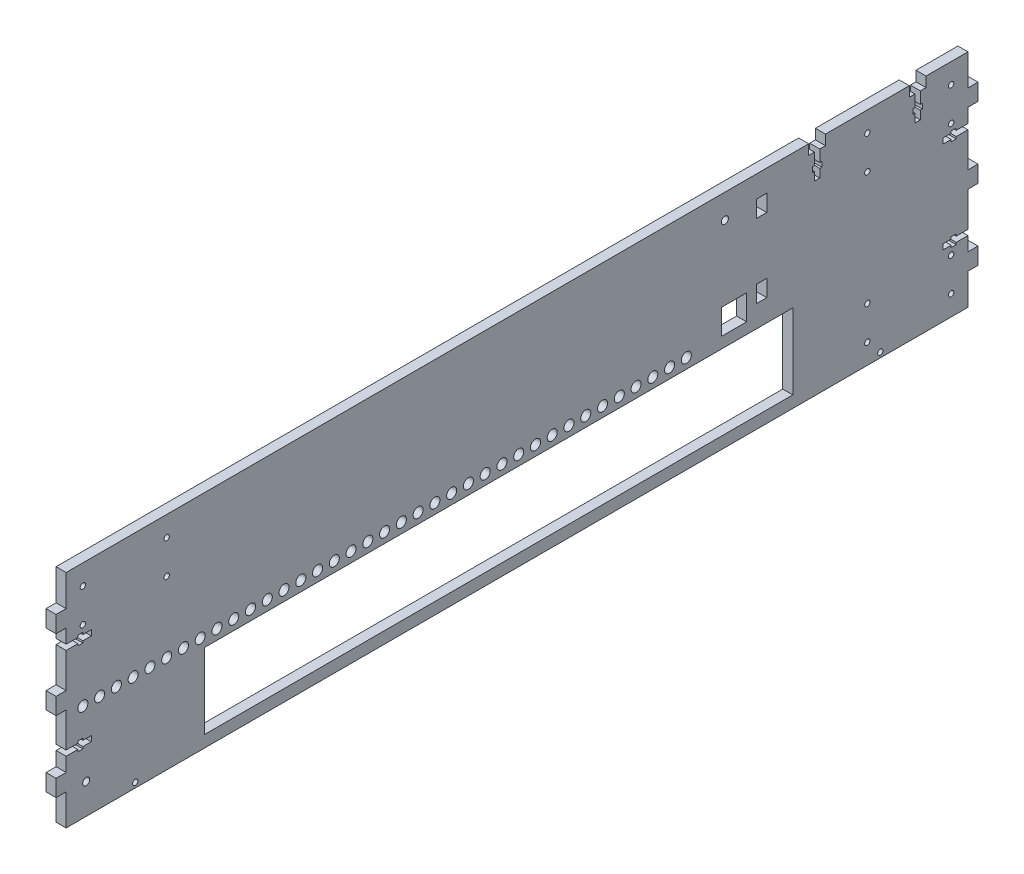
SolidWorks part; units mm, degrees
ref_plane "Front Plane" through (0, 0, 0) normal (0, 0, 1) x (1, 0, 0)
ref_plane "Top Plane" through (0, 0, 0) normal (0, 1, 0) x (1, 0, 0)
ref_plane "Right Plane" through (0, 0, 0) normal (1, 0, 0) x (0, 0, -1)
sketch "Sketch1" plane through (0, 0, 0) normal (1, 0, 0) x (0, 0, -1)
  line L1 (-269, -66) -> (269, -66)
  line L2 (-269, -66) -> (-269, 66)
  line L3 (-269, 66) -> (269, 66)
  line L4 (269, -66) -> (269, 66)
  line L5 (-269, -66) -> (269, 66) construction
  line L6 (-269, 66) -> (269, -66) construction
  point P0 (0, 0)
  dimension "D1" = 132
  dimension "D2" = 538
extrude "Boss-Extrude1" add sketch "Sketch1" along normal blind 6
sketch "Sketch4" plane through (0, 0, 269) normal (0, 0, 1) x (1, 0, 0)
  line L0 (0, 66) -> (0, -66) construction
  line L1 (0, 47.3321) -> (6, 47.3321)
  line L2 (0, 47.3321) -> (0, 37.3321)
  line L3 (0, 37.3321) -> (6, 37.3321)
  line L4 (6, 47.3321) -> (6, 37.3321)
  line L5 (6, 66) -> (6, -66) construction
  line L6 (0, 37.3321) -> (6, 37.3321) construction
  line L7 (0, -66) -> (0, 66) construction
  line L8 (6, 47.3321) -> (0, 47.3321) construction
  line L9 (0, -5) -> (6, -5) construction
  line L10 (0, -5) -> (6, -5)
  line L11 (0, -5) -> (0, 5)
  line L12 (0, 5) -> (6, 5)
  line L13 (6, -5) -> (6, 5)
  line L14 (6, -66) -> (6, 66) construction
  line L15 (6, 5) -> (0, 5) construction
  line L16 (6, -37.3321) -> (0, -37.3321) construction
  line L17 (0, -47.3321) -> (6, -47.3321)
  line L18 (0, -47.3321) -> (0, -37.3321)
  line L19 (0, -37.3321) -> (6, -37.3321)
  line L20 (6, -47.3321) -> (6, -37.3321)
  line L21 (0, -47.3321) -> (6, -47.3321) construction
extrude "Boss-Extrude2" add sketch "Sketch4" along normal blind 6 contours L11 L12 L13 L10
sketch "Sketch5" plane through (0, 0, 0) normal (-1, 0, 0) x (0, 0, 1)
  line L1 (269, 28.9321) -> (269, 25.7321) construction
  line L3 (269, 28.9321) -> (269, 25.7321) construction
  line L4 (269, -25.7321) -> (269, -28.9321) construction
  line L5 (269, -25.7321) -> (269, -28.9321) construction
  line L6 (269, 27.3321) -> (254, 27.3321) construction
  line L7 (269, -27.3321) -> (254, -27.3321) construction
  line L8 (269, -25.7321) -> (262, -25.7321)
  line L9 (269, 28.9321) -> (262, 28.9321)
  line L10 (269, -28.9321) -> (262, -28.9321)
  line L11 (269, 25.7321) -> (262, 25.7321)
  line L12 (269, -25.7321) -> (269, -28.9321)
  line L13 (254, -25.7321) -> (254, -28.9321)
  line L14 (269, 28.9321) -> (269, 25.7321)
  line L15 (254, 28.9321) -> (254, 25.7321)
  line L16 (259, 25.7321) -> (254, 25.7321)
  line L17 (262, 24.5321) -> (259, 24.5321)
  line L18 (262, 24.5321) -> (262, 25.7321)
  line L19 (262, 30.1321) -> (259, 30.1321)
  line L20 (259, 24.5321) -> (259, 25.7321)
  line L21 (262, 24.5321) -> (259, 30.1321) construction
  line L22 (262, 30.1321) -> (259, 24.5321) construction
  line L23 (262, -30.1321) -> (259, -30.1321)
  line L24 (262, -30.1321) -> (262, -28.9321)
  line L25 (262, -24.5321) -> (259, -24.5321)
  line L26 (259, -30.1321) -> (259, -28.9321)
  line L27 (262, -30.1321) -> (259, -24.5321) construction
  line L28 (262, -24.5321) -> (259, -30.1321) construction
  line L29 (269, 25.7321) -> (254, 25.7321) construction
  line L30 (262, 28.9321) -> (262, 30.1321)
  line L31 (259, 28.9321) -> (254, 28.9321)
  line L32 (269, 28.9321) -> (254, 28.9321) construction
  line L33 (259, 28.9321) -> (259, 30.1321)
  line L34 (259, -25.7321) -> (254, -25.7321)
  line L35 (269, -25.7321) -> (254, -25.7321) construction
  line L36 (259, -25.7321) -> (259, -24.5321)
  line L37 (259, -28.9321) -> (254, -28.9321)
  line L38 (269, -28.9321) -> (254, -28.9321) construction
  line L39 (262, -25.7321) -> (262, -24.5321)
  point P20 (260.5, 27.3321)
  point P25 (260.5, -27.3321)
  dimension "D3" = 1.6
  dimension "D4" = 7
  dimension "D5" = 3
  dimension "D6" = 5.6
  dimension "D1" = 15
  dimension "D7" = 7
  dimension "D8" = 3
  dimension "D9" = 5.6
  dimension "D2" = 1.6
extrude "Cut-Extrude3" cut sketch "Sketch5" against normal up to next
sketch "Sketch6" plane through (0, 0, -269) normal (0, 0, -1) x (-1, 0, 0)
  line L0 (0, 47.3321) -> (0, 37.3321) construction
  line L1 (0, 37.3321) -> (-6, 37.3321) construction
  line L2 (-6, 37.3321) -> (-6, 47.3321) construction
  line L3 (-6, 47.3321) -> (0, 47.3321) construction
  line L4 (0, 5) -> (0, -5) construction
  line L5 (0, -5) -> (-6, -5) construction
  line L6 (-6, -5) -> (-6, 5) construction
  line L7 (-6, 5) -> (0, 5) construction
  line L8 (0, -37.3321) -> (0, -47.3321) construction
  line L9 (0, -47.3321) -> (-6, -47.3321) construction
  line L10 (-6, -47.3321) -> (-6, -37.3321) construction
  line L11 (-6, -37.3321) -> (0, -37.3321) construction
  line L12 (0, 47.3321) -> (0, 37.3321)
  line L13 (0, 37.3321) -> (-6, 37.3321)
  line L14 (-6, 37.3321) -> (-6, 47.3321)
  line L15 (-6, 47.3321) -> (0, 47.3321)
  line L16 (0, 5) -> (0, -5)
  line L17 (0, -5) -> (-6, -5)
  line L18 (-6, -5) -> (-6, 5)
  line L19 (-6, 5) -> (0, 5)
  line L20 (0, -37.3321) -> (0, -47.3321)
  line L21 (0, -47.3321) -> (-6, -47.3321)
  line L22 (-6, -47.3321) -> (-6, -37.3321)
  line L23 (-6, -37.3321) -> (0, -37.3321)
extrude "Boss-Extrude3" add sketch "Sketch6" along normal blind 6
sketch "Sketch7" plane through (0, 0, 0) normal (-1, 0, 0) x (0, 0, 1)
  line L0 (262, 25.7321) -> (269, 25.7321) construction
  line L2 (262, 25.7321) -> (262, 24.5321) construction
  line L3 (259, 24.5321) -> (262, 24.5321) construction
  line L4 (259, 25.7321) -> (259, 24.5321) construction
  line L5 (254, 25.7321) -> (259, 25.7321) construction
  line L6 (254, 25.7321) -> (254, 28.9321) construction
  line L7 (254, 28.9321) -> (259, 28.9321) construction
  line L8 (259, 30.1321) -> (259, 28.9321) construction
  line L9 (259, 30.1321) -> (262, 30.1321) construction
  line L10 (262, 30.1321) -> (262, 28.9321) construction
  line L11 (262, 28.9321) -> (269, 28.9321) construction
  line L12 (262, 25.7321) -> (269, 25.7321) construction
  line L13 (262, 25.7321) -> (262, 24.5321) construction
  line L14 (259, 24.5321) -> (262, 24.5321) construction
  line L15 (259, 25.7321) -> (259, 24.5321) construction
  line L16 (254, 25.7321) -> (259, 25.7321) construction
  line L17 (254, 25.7321) -> (254, 28.9321) construction
  line L18 (254, 28.9321) -> (259, 28.9321) construction
  line L19 (259, 30.1321) -> (259, 28.9321) construction
  line L20 (259, 30.1321) -> (262, 30.1321) construction
  line L21 (262, 30.1321) -> (262, 28.9321) construction
  line L22 (262, 28.9321) -> (269, 28.9321) construction
  line L23 (254, -28.9321) -> (259, -28.9321) construction
  line L24 (259, -28.9321) -> (259, -30.1321) construction
  line L25 (259, -30.1321) -> (262, -30.1321) construction
  line L26 (262, -28.9321) -> (262, -30.1321) construction
  line L27 (262, -28.9321) -> (269, -28.9321) construction
  line L28 (262, -25.7321) -> (269, -25.7321) construction
  line L29 (262, -24.5321) -> (262, -25.7321) construction
  line L30 (259, -24.5321) -> (262, -24.5321) construction
  line L31 (259, -24.5321) -> (259, -25.7321) construction
  line L32 (254, -25.7321) -> (259, -25.7321) construction
  line L33 (254, -28.9321) -> (254, -25.7321) construction
  line L34 (254, -28.9321) -> (259, -28.9321) construction
  line L35 (259, -28.9321) -> (259, -30.1321) construction
  line L36 (259, -30.1321) -> (262, -30.1321) construction
  line L37 (262, -28.9321) -> (262, -30.1321) construction
  line L38 (262, -28.9321) -> (269, -28.9321) construction
  line L39 (262, -25.7321) -> (269, -25.7321) construction
  line L40 (262, -24.5321) -> (262, -25.7321) construction
  line L41 (259, -24.5321) -> (262, -24.5321) construction
  line L42 (259, -24.5321) -> (259, -25.7321) construction
  line L43 (254, -25.7321) -> (259, -25.7321) construction
  line L44 (254, -28.9321) -> (254, -25.7321) construction
  line L45 (0, 0) -> (0, 57.5645) construction
  line L46 (-254, -28.9321) -> (-254, -25.7321)
  line L47 (-254, -25.7321) -> (-259, -25.7321)
  line L48 (-259, -24.5321) -> (-259, -25.7321)
  line L49 (-259, -24.5321) -> (-262, -24.5321)
  line L50 (-262, -24.5321) -> (-262, -25.7321)
  line L51 (-262, -25.7321) -> (-269, -25.7321)
  line L52 (-262, -28.9321) -> (-269, -28.9321)
  line L53 (-262, -28.9321) -> (-262, -30.1321)
  line L54 (-259, -30.1321) -> (-262, -30.1321)
  line L55 (-259, -28.9321) -> (-259, -30.1321)
  line L56 (-254, -28.9321) -> (-259, -28.9321)
  line L57 (-262, 28.9321) -> (-269, 28.9321)
  line L58 (-262, 30.1321) -> (-262, 28.9321)
  line L59 (-259, 30.1321) -> (-262, 30.1321)
  line L60 (-259, 30.1321) -> (-259, 28.9321)
  line L61 (-254, 28.9321) -> (-259, 28.9321)
  line L62 (-254, 25.7321) -> (-254, 28.9321)
  line L63 (-254, 25.7321) -> (-259, 25.7321)
  line L64 (-259, 25.7321) -> (-259, 24.5321)
  line L65 (-259, 24.5321) -> (-262, 24.5321)
  line L66 (-262, 25.7321) -> (-262, 24.5321)
  line L67 (-262, 25.7321) -> (-269, 25.7321)
  line L68 (-269, 28.9321) -> (-269, 25.7321)
  line L69 (-269, -25.7321) -> (-269, -28.9321)
extrude "Cut-Extrude4" cut sketch "Sketch7" against normal up to next
sketch "Sketch8" plane through (0, 0, 0) normal (-1, 0, 0) x (0, 0, 1)
  line L0 (186, -14.55) -> (-164, -14.55) construction
  line L1 (186, -14.55) -> (-164, -14.55) construction
  line L2 (186, -14.55) -> (186, -59) construction
  line L3 (186, -14.55) -> (186, -59) construction
  line L186 (-164, -14.55) -> (-164, -59) construction
  line L187 (-164, -59) -> (186, -59) construction
  line L188 (186.5, -14.05) -> (186.5, -59)
  line L189 (186.5, -14.05) -> (-164.5, -14.05)
  line L190 (-164.5, -14.05) -> (-164.5, -59)
  line L191 (-164.5, -59) -> (186.5, -59)
  dimension "D1" = 0.5
extrude "Cut-Extrude5" cut sketch "Sketch8" against normal up to next
sketch "Sketch11" plane through (6, 0, 0) normal (1, 0, 0) x (0, 0, -1)
  line L0 (149, 43) -> (149, 53) construction
  line L1 (149, 53) -> (143, 53) construction
  line L2 (143, 53) -> (143, 43) construction
  line L3 (143, 43) -> (149, 43) construction
  line L4 (149, -1) -> (149, 9) construction
  line L5 (149, 9) -> (143, 9) construction
  line L6 (143, 9) -> (143, -1) construction
  line L7 (143, -1) -> (149, -1) construction
  line L8 (149, 43) -> (149, 53)
  line L9 (149, 53) -> (143, 53)
  line L10 (143, 53) -> (143, 43)
  line L11 (143, 43) -> (149, 43)
  line L12 (149, -1) -> (149, 9)
  line L13 (149, 9) -> (143, 9)
  line L14 (143, 9) -> (143, -1)
  line L15 (143, -1) -> (149, -1)
extrude "Cut-Extrude8" cut sketch "Sketch11" against normal up to next
sketch "Sketch12" plane through (0, 0, 0) normal (-1, 0, 0) x (0, 0, 1)
  line L0 (-143, 53) -> (-143, 43) construction
  line L1 (-269, 66) -> (269, 66) construction
  circle A0 centre (-124, 51.5) radius 2.1
  dimension "D1" = 19
  dimension "D3" = 4.2
  dimension "D2" = 14.5
extrude "Cut-Extrude9" cut sketch "Sketch12" against normal up to next
sketch "Sketch13" plane through (0, 66, 0) normal (0, 1, 0) x (1, 0, 0)
  line L0 (6, 269) -> (6, -269) construction
  line L1 (0, 234) -> (6, 234)
  line L2 (0, 234) -> (0, 244)
  line L3 (0, 244) -> (6, 244)
  line L4 (6, 234) -> (6, 244)
  line L5 (0, 234) -> (6, 244) construction
  line L6 (0, 244) -> (6, 234) construction
  line L7 (6, 244) -> (0, 244) construction
  line L8 (6, 184) -> (0, 184) construction
  line L9 (0, 174) -> (6, 174)
  line L10 (0, 174) -> (0, 184)
  line L11 (0, 184) -> (6, 184)
  line L12 (6, 174) -> (6, 184)
  line L13 (0, 174) -> (6, 184) construction
  line L14 (0, 184) -> (6, 174) construction
  point P0 (3, 239)
  point P10 (3, 179)
extrude "Cut-Extrude10" cut sketch "Sketch13" against normal blind 6
sketch "Sketch14" plane through (0, 0, 0) normal (-1, 0, 0) x (0, 0, 1)
  circle A0 centre (259, -8) radius 3 construction
  circle A1 centre (259, -8) radius 3
  circle A2 centre (249, -8) radius 3
  circle A3 centre (239, -8) radius 3
  circle A4 centre (229, -8) radius 3
  circle A5 centre (219, -8) radius 3
  circle A6 centre (209, -8) radius 3
  circle A7 centre (199, -8) radius 3
  circle A8 centre (189, -8) radius 3
  circle A9 centre (179, -8) radius 3
  circle A10 centre (169, -8) radius 3
  circle A11 centre (159, -8) radius 3
  circle A12 centre (149, -8) radius 3
  circle A13 centre (139, -8) radius 3
  circle A14 centre (129, -8) radius 3
  circle A15 centre (119, -8) radius 3
  circle A16 centre (109, -8) radius 3
  circle A17 centre (99, -8) radius 3
  circle A18 centre (89, -8) radius 3
  circle A19 centre (79, -8) radius 3
  circle A20 centre (69, -8) radius 3
  circle A21 centre (59, -8) radius 3
  circle A22 centre (49, -8) radius 3
  circle A23 centre (39, -8) radius 3
  circle A24 centre (29, -8) radius 3
  circle A25 centre (19, -8) radius 3
  circle A26 centre (9, -8) radius 3
  circle A27 centre (-1, -8) radius 3
  circle A28 centre (-11, -8) radius 3
  circle A29 centre (-21, -8) radius 3
  circle A30 centre (-31, -8) radius 3
  circle A31 centre (-41, -8) radius 3
  circle A32 centre (-51, -8) radius 3
  circle A33 centre (-61, -8) radius 3
  circle A34 centre (-71, -8) radius 3
  circle A35 centre (-81, -8) radius 3
  circle A36 centre (-91, -8) radius 3
  circle A37 centre (-101, -8) radius 3
  dimension "D1" = 37
extrude "Cut-Extrude11" cut sketch "Sketch14" against normal up to next (6 mm away)
sketch "Sketch15" plane through (6, 0, 0) normal (1, 0, 0) x (0, 0, -1)
  line L0 (179, 60) -> (179, 45) construction
  line L1 (174, 60) -> (184, 60) construction
  line L2 (239, 60) -> (239, 45) construction
  line L3 (234, 60) -> (244, 60) construction
  line L4 (179, 45) -> (239, 45) construction
  line L5 (209, 45) -> (209, 66) construction
  line L6 (234, 66) -> (184, 66) construction
  line L7 (177.4, 60) -> (177.4, 53)
  line L8 (180.6, 60) -> (180.6, 53)
  line L9 (177.4, 60) -> (180.6, 60)
  line L10 (177.4, 45) -> (180.6, 45)
  line L11 (180.6, 50) -> (181.8, 50)
  line L12 (176.2, 53) -> (177.4, 53)
  line L13 (176.2, 53) -> (176.2, 50)
  line L14 (176.2, 50) -> (177.4, 50)
  line L15 (181.8, 53) -> (181.8, 50)
  line L16 (176.2, 53) -> (181.8, 50) construction
  line L17 (176.2, 50) -> (181.8, 53) construction
  line L18 (180.6, 53) -> (181.8, 53)
  line L19 (177.4, 50) -> (177.4, 45)
  line L20 (177.4, 60) -> (177.4, 45) construction
  line L21 (180.6, 50) -> (180.6, 45)
  line L22 (180.6, 60) -> (180.6, 45) construction
  line L23 (241.8, 50) -> (236.2, 53) construction
  line L24 (241.8, 53) -> (236.2, 50) construction
  line L25 (239, 60) -> (239, 45) construction
  line L26 (237.4, 50) -> (237.4, 45)
  line L27 (240.6, 50) -> (240.6, 45)
  line L28 (237.4, 53) -> (236.2, 53)
  line L29 (236.2, 53) -> (236.2, 50)
  line L30 (241.8, 50) -> (240.6, 50)
  line L31 (241.8, 53) -> (241.8, 50)
  line L32 (241.8, 53) -> (240.6, 53)
  line L33 (237.4, 50) -> (236.2, 50)
  line L34 (240.6, 45) -> (237.4, 45)
  line L35 (240.6, 60) -> (237.4, 60)
  line L36 (237.4, 60) -> (237.4, 53)
  line L37 (240.6, 60) -> (240.6, 53)
  point P16 (179, 51.5)
  point P37 (239, 51.5)
  dimension "D3" = 15
  dimension "D4" = 7
  dimension "D5" = 3
  dimension "D6" = 5.6
  dimension "D1" = 1.6
  dimension "D2" = 1.6
extrude "Cut-Extrude12" cut sketch "Sketch15" against normal up to next
sketch "Sketch17" plane through (6, 0, 0) normal (1, 0, 0) x (0, 0, -1)
  circle A0 centre (-257, -48) radius 2.1 construction
  circle A1 centre (-257, -48) radius 2.1
extrude "Cut-Extrude14" cut sketch "Sketch17" against normal through all
sketch "Sketch18" plane through (6, 0, 0) normal (1, 0, 0) x (0, 0, -1)
  line L0 (-186.5, -59) -> (-269, -59) construction
  line L1 (-269, -47.3321) -> (-269, -66) construction
  line L2 (-227.75, -59) -> (-227.75, -66) construction
  line L3 (-269, -66) -> (269, -66) construction
  line L4 (164.5, -59) -> (269, -59) construction
  line L5 (269, -66) -> (269, -47.3321) construction
  line L6 (216.75, -59) -> (216.75, -66) construction
  circle A0 centre (-227.75, -63) radius 1.6
  circle A1 centre (216.75, -63) radius 1.6
  dimension "D1" = 3.2
  dimension "D2" = 3
extrude "Cut-Extrude15" cut sketch "Sketch18" against normal through all
sketch "Sketch19" plane through (6, 0, 0) normal (1, 0, 0) x (0, 0, -1)
  circle A1 centre (259, -34) radius 1.6
  circle A2 centre (259, -34) radius 1.6
  circle A3 centre (259, 54) radius 1.6
  circle A5 centre (259, 54) radius 1.6
  circle A7 centre (259, -54) radius 1.6
  circle A8 centre (259, -54) radius 1.6
  circle A11 centre (209, -54) radius 1.6
  circle A12 centre (209, -54) radius 1.6
  circle A15 centre (209, -34) radius 1.6
  circle A16 centre (209, -34) radius 1.6
  circle A24 centre (209, 34) radius 1.6
  circle A25 centre (209, 34) radius 1.6
  circle A30 centre (209, 54) radius 1.6
  circle A31 centre (209, 54) radius 1.6
  circle A32 centre (259, 34) radius 1.6
  circle A33 centre (259, 34) radius 1.6
  circle A56 centre (-209, 34) radius 1.6 construction
  circle A57 centre (-259, 34) radius 1.6 construction
  circle A58 centre (-209, 54) radius 1.6 construction
  circle A59 centre (-259, 54) radius 1.6 construction
  circle A60 centre (-209, 34) radius 1.6
  circle A61 centre (-259, 34) radius 1.6
  circle A62 centre (-209, 54) radius 1.6
  circle A63 centre (-259, 54) radius 1.6
  dimension "D1" = 0
  dimension "D2" = 0
  dimension "D5" = 0
  dimension "D7" = 0
  dimension "D9" = 0
  dimension "D12" = 0
  dimension "D15" = 0
  dimension "D16" = 0
extrude "Cut-Extrude16" cut sketch "Sketch19" against normal through all
sketch "Sketch20" plane through (6, 0, 0) normal (1, 0, 0) x (0, 0, -1)
  line L0 (-269, 22) -> (269, 22) construction
  line L1 (-269, 22) -> (269, 22) construction
  line L2 (-269, -22) -> (269, -22) construction
  line L3 (-269, -22) -> (269, -22) construction
  line L4 (137, 22) -> (137, -22) construction
  line L5 (143, 9) -> (143, -1) construction
  line L6 (137, 0) -> (122, 0) construction
  line L7 (137, 7.5) -> (122, 7.5)
  line L8 (137, -7.5) -> (122, -7.5)
  line L9 (137, 7.5) -> (137, -7.5)
  line L10 (122, 7.5) -> (122, -7.5)
  point P8 (143, 4)
  dimension "D1" = 6
  dimension "D2" = 15
  dimension "D3" = 7.5
  dimension "D4" = 7.5
extrude "Cut-Extrude17" cut sketch "Sketch20" against normal through all
